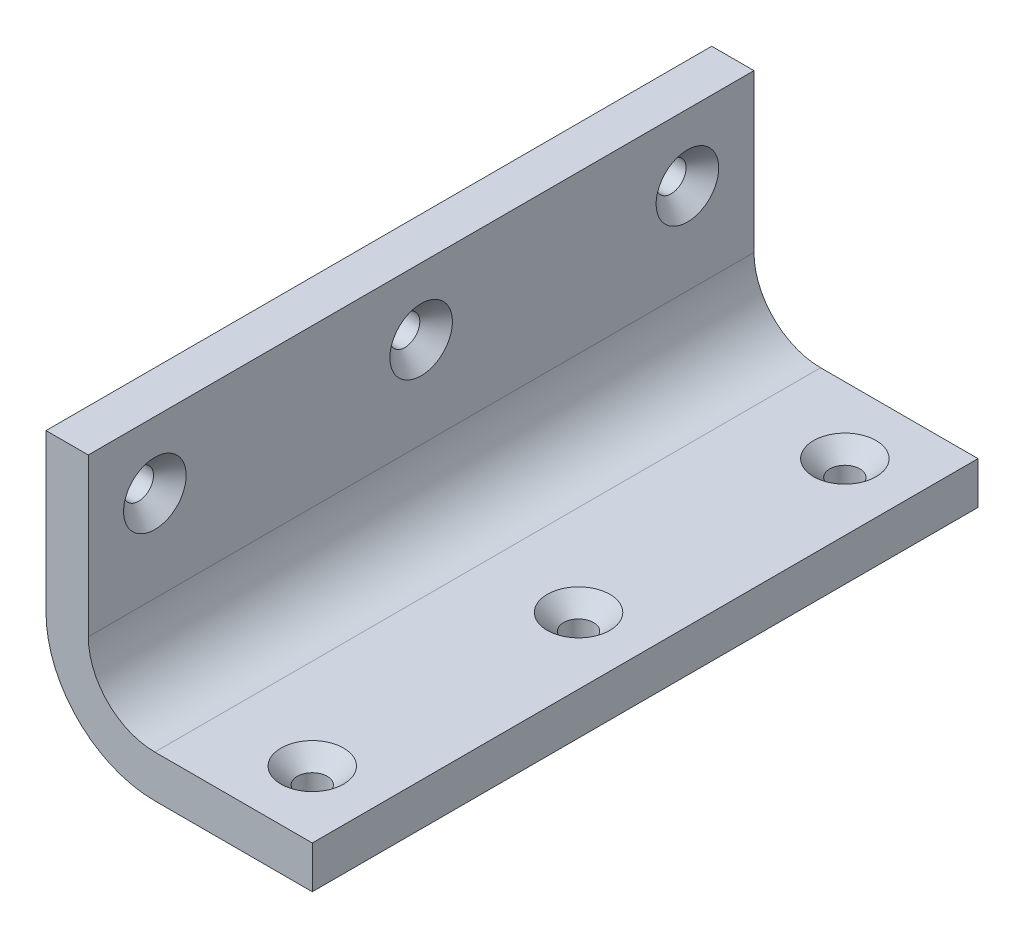
SolidWorks part; units mm, degrees
ref_plane "Front Plane" through (0, 0, 0) normal (0, 0, 1) x (1, 0, 0)
ref_plane "Top Plane" through (0, 0, 0) normal (0, 1, 0) x (1, 0, 0)
ref_plane "Right Plane" through (0, 0, 0) normal (1, 0, 0) x (0, 0, -1)
sketch "Sketch1" plane through (0, 0, 0) normal (0, 0, 1) x (1, 0, 0)
  line L0 (0, 40) -> (0, 16.35)
  line L1 (16.35, 0) -> (40, 0)
  line L2 (40, 0) -> (40, 6.35)
  line L3 (40, 6.35) -> (16.35, 6.35)
  line L4 (6.35, 16.35) -> (6.35, 40)
  line L5 (6.35, 40) -> (0, 40)
  arc A0 (6.35, 16.35) -> (16.35, 6.35) centre (16.35, 16.35) ccw
  arc A1 (0, 16.35) -> (16.35, 0) centre (16.35, 16.35) ccw
  point P11 (0, 0)
  dimension "D2" = 10
  dimension "D4" = 16.35
  dimension "D1" = 40
  dimension "D3" = 6.35
extrude "Boss-Extrude1" add sketch "Sketch1" along normal blind 100
hole_wizard "CSK for M4 Flat Head Machine Screw1" positions "Sketch3" profile "Sketch2" countersink size "M4" standard "ANSI Metric" end condition through all
sketch "Sketch3" plane through (0, 6.35, 0) normal (0, 1, 0) x (1, 0, 0)
  line L0 (40, -100) -> (16.35, -100) construction
  line L1 (40, -100) -> (40, 0) construction
  point P0 (30, -90)
  point P2 (30, -50)
  point P4 (30, -10)
  dimension "D1" = 40
  dimension "D2" = 40
  dimension "D3" = 10
  dimension "D4" = 10
sketch "Sketch2" plane through (30, 6.35, 90) normal (1, 0, 0) x (0, 0, 1)
  line L0 (0, 0) -> (0, 6.35)
  line L1 (0, 6.35) -> (2.25, 6.35)
  line L2 (2.25, 6.35) -> (2.25, 2.45)
  line L3 (2.25, 2.45) -> (4.7, 0)
  line L5 (4.7, 0) -> (0, 0)
  line L6 (-2.25, 2.45) -> (-4.7, 0) construction
  line L11 (0, -6.35) -> (0, 107.95) construction
  dimension "Thru Hole Dia." = 4.5
  dimension "Thru Hole Depth" = 6.35
  dimension "Near C'Sink Dia." = 9.4
  dimension "Near C'Sink Angle" = 90
hole_wizard "CSK for M4 Flat Head Machine Screw4" positions "Sketch8" profile "Sketch9" countersink size "M4" standard "ANSI Metric" end condition through all
sketch "Sketch8" plane through (6.35, 0, 0) normal (1, 0, 0) x (0, -1, 0)
  line L1 (-16.35, 0) -> (-40, 0) construction
  line L2 (-30, -90) -> (-30, -10) construction
  line L4 (-40, -100) -> (-40, 0) construction
  point P0 (-30, -90)
  point P2 (-30, -50)
  point P4 (-30, -10)
  dimension "D1" = 40
  dimension "D2" = 40
  dimension "D3" = 10
  dimension "D4" = 10
sketch "Sketch9" plane through (6.35, 30, 90) normal (0, 1, 0) x (0, 0, -1)
  line L0 (0, 0) -> (0, 6.35)
  line L1 (0, 6.35) -> (2.25, 6.35)
  line L2 (2.25, 6.35) -> (2.25, 2.45)
  line L3 (2.25, 2.45) -> (4.7, 0)
  line L5 (4.7, 0) -> (0, 0)
  line L6 (-2.25, 2.45) -> (-4.7, 0) construction
  line L11 (0, -6.35) -> (0, 107.95) construction
  dimension "Thru Hole Dia." = 4.5
  dimension "Thru Hole Depth" = 6.35
  dimension "Near C'Sink Dia." = 9.4
  dimension "Near C'Sink Angle" = 90
equation "\"connector_D1\" = 70 'the big holes diameter"
equation "\"mtg_hole_D\" = 5.5 'mounting holes"
equation "\"mtg_dfc\" = 40 'mounting hole distance from center"
equation "\"plate_thickness\" = 6.35 'thickness of the plate "
equation "\"t_height\" = 150"
equation "\"t_width\" = 240"
equation "\"t_length\" = 282"
equation "\"plate_hole_from_edge\" = 9"
equation "\"plate_spacing\" = 1"
equation "\"front_plate_height\" = \"t_height\" + 38"
equation "\"front_plate_width\" = \"t_width\" + 38"
equation "\"side_plate_height\" = \"front_plate_height\""
equation "\"side_plate_length\" = \"t_length\" + 38"
equation "\"top_plate_width\" = \"front_plate_width\""
equation "\"top_plate_length\" = \"side_plate_length\""
equation "\"locomotion_length\" = \"t_length\""
equation "\"locomotion_width\" = \"t_width\""
equation "\"locomotion_height\" = 40"
equation "\"D3@Sketch1\"=\"plate_thickness\""
equation "\"D4@Sketch1\"=\"D2@Sketch1\"+\"D3@Sketch1\""
equation "\"D2@Sketch3\"=\"D1@Sketch3\""
equation "\"D3@Sketch3\"=50 - \"D1@Sketch3\""
equation "\"D3@Sketch8\"=50-\"D2@Sketch8\""
equation "\"itx_support_t_slot_length\" = \"t_width\" + (2 * 20.5)"
equation "\"itx_mtg_hole_spacing\" = 40"
equation "\"D1@Sketch3\"=\"itx_mtg_hole_spacing\""
equation "\"D1@Sketch8\"=\"itx_mtg_hole_spacing\""
equation "\"D2@Sketch8\"=\"itx_mtg_hole_spacing\""
